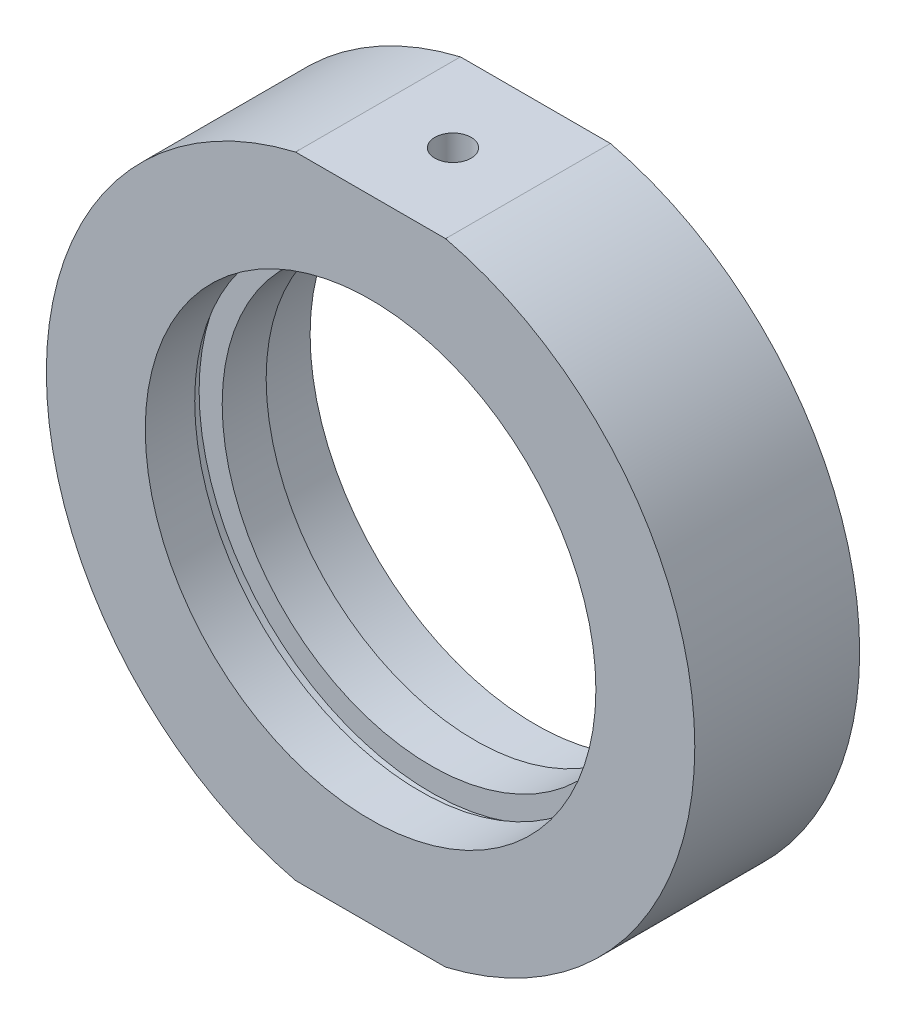
SolidWorks part; units mm, degrees
ref_plane "前视基准面" through (0, 0, 0) normal (0, 0, 1) x (1, 0, 0)
ref_plane "上视基准面" through (0, 0, 0) normal (0, 1, 0) x (1, 0, 0)
ref_plane "右视基准面" through (0, 0, 0) normal (1, 0, 0) x (0, 0, -1)
sketch "草图1" plane through (0, 0, 0) normal (0, 1, 0) x (1, 0, 0)
  line L0 (0, 31.9391) -> (0, -26.491) construction
  line L1 (29.5, 7.5) -> (29.5, -7.5)
  line L3 (21.1, 2) -> (21.1, 3)
  line L4 (21.1, 3) -> (20.5, 3)
  line L6 (29.5, -7.5) -> (20.5, -7.5)
  line L7 (20.5, -7.5) -> (20.5, -3)
  line L8 (21.1, -2) -> (19, -2)
  line L9 (19, -2) -> (19, 2)
  line L10 (19, 2) -> (21.1, 2)
  line L11 (20.5, 3) -> (20.5, 7.5)
  line L12 (20.5, 7.5) -> (29.5, 7.5)
  line L13 (21.1, -2) -> (21.1, -3)
  line L14 (21.1, -3) -> (20.5, -3)
  line L17 (35.331, 0) -> (-5.0345, 0) construction
  point P6 (19, 0)
  dimension "D2" = 19
  dimension "D3" = 20.5
  dimension "D4" = 20.5
  dimension "D5" = 15
  dimension "D6" = 5.5
  dimension "D7" = 5.5
  dimension "D8" = 21.1
  dimension "D9" = 29.5
  dimension "D10" = 21.1
  dimension "D11" = 1
  dimension "D12" = 1
  dimension "D13" = 7.5
  dimension "D18" = 0
revolve "旋转1" add sketch "草图1" angle 360 about L0
cosmetic thread "装饰螺纹线1" parameters "D2"=42
cosmetic thread "装饰螺纹线2" parameters "D2"=42
sketch "草图2" plane through (0, 0, 7.5) normal (0, 0, 1) x (1, 0, 0)
  line L0 (0, 0) -> (43.1523, 0) construction
  line L1 (-33.152, 37.9489) -> (30.8698, 37.9489)
  line L2 (-33.152, 37.9489) -> (-33.152, 28.7)
  line L3 (-33.152, 28.7) -> (30.8698, 28.7)
  line L4 (30.8698, 37.9489) -> (30.8698, 28.7)
  line L5 (30.8698, -37.9489) -> (30.8698, -28.7)
  line L6 (-33.152, -28.7) -> (30.8698, -28.7)
  line L7 (-33.152, -37.9489) -> (-33.152, -28.7)
  line L8 (-33.152, -37.9489) -> (30.8698, -37.9489)
  dimension "D1" = 28.7
extrude "切除-拉伸1" cut sketch "草图2" against normal blind 49
sketch "草图10" plane through (0, 0, 0) normal (0, 0, 1) x (1, 0, 0)
  line L0 (0, 28.7) -> (0, -28.7)
  line L1 (-6.8235, 28.7) -> (6.8235, 28.7) construction
  line L2 (-6.8235, -28.7) -> (6.8235, -28.7) construction
  line L3 (0, 0) -> (-25.5477, 14.75)
  line L4 (0, 0) -> (25.5477, 14.75)
  arc A2 (6.8235, -28.7) -> (6.8235, 28.7) centre (0, 0) ccw construction
  arc A3 (-6.8235, 28.7) -> (-6.8235, -28.7) centre (0, 0) ccw construction
  arc A4 (25.5477, 14.75) -> (6.8235, 28.7) centre (0, 0) ccw
  arc A5 (-6.8235, 28.7) -> (-25.5477, 14.75) centre (0, 0) ccw
  dimension "D1" = 60
  dimension "D2" = 60
hole_wizard "M4 螺纹孔2" positions "草图15" profile "草图16" tap size "M4" standard "ISO"
sketch "草图15" plane through (0, 28.7, 0) normal (0, 1, 0) x (1, 0, 0)
  point P0 (0, 0)
sketch "草图16" plane through (0, 28.7, 0) normal (1, 0, 0) x (0, 0, 1)
  line L0 (0, 0) -> (0, 6.4914)
  line L1 (0, 6.4914) -> (1.65, 5.5)
  line L2 (1.65, 5.5) -> (1.65, 0)
  line L5 (1.65, 0) -> (0, 0)
  line L10 (0, 6.4914) -> (-1.65, 5.5) construction
  line L11 (0, -6.35) -> (0, 107.95) construction
  dimension "螺纹孔钻头直径" = 3.3
  dimension "螺纹孔钻头深度" = 5.5
  dimension "导头角度" = 118
cosmetic thread "孔螺蚊线6" parameters "D1"=5.5, "D2"=4
hole_wizard "M6 螺纹孔2" positions "草图17" profile "草图18" tap size "M6" standard "ISO"
sketch "草图17" plane through (0, -28.7, 0) normal (0, -1, 0) x (-1, 0, 0)
  point P0 (0, 0)
sketch "草图18" plane through (0, -28.7, 0) normal (1, 0, 0) x (0, 0, -1)
  line L0 (0, 0) -> (0, 7.0022)
  line L1 (0, 7.0022) -> (2.5, 5.5)
  line L2 (2.5, 5.5) -> (2.5, 0)
  line L5 (2.5, 0) -> (0, 0)
  line L10 (0, 7.0022) -> (-2.5, 5.5) construction
  line L11 (0, -6.35) -> (0, 107.95) construction
  dimension "螺纹孔钻头直径" = 5
  dimension "螺纹孔钻头深度" = 5.5
  dimension "导头角度" = 118
cosmetic thread "孔螺蚊线7" parameters "D1"=5.5, "D2"=6
